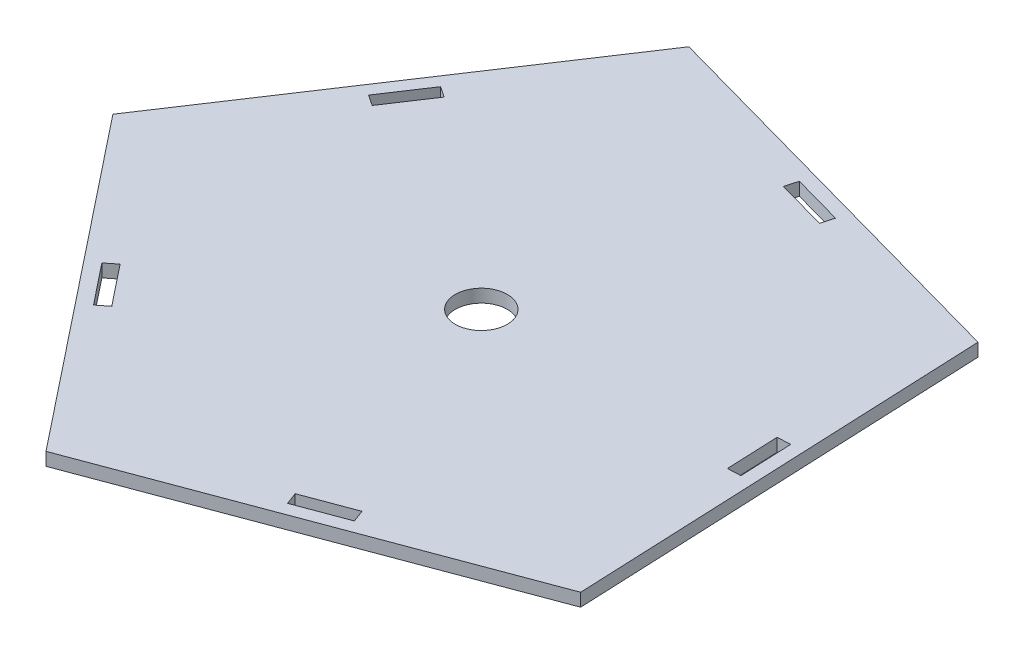
SolidWorks part; units mm, degrees
ref_plane "Front Plane" through (0, 0, 0) normal (0, 0, 1) x (1, 0, 0)
ref_plane "Top Plane" through (0, 0, 0) normal (0, 1, 0) x (1, 0, 0)
ref_plane "Right Plane" through (0, 0, 0) normal (1, 0, 0) x (0, 0, -1)
sketch "Sketch1" plane through (0, 0, 0) normal (0, 1, 0) x (1, 0, 0)
  line L1 (-20.8753, -32.8264) -> (-29.6171, 170.1854)
  line L2 (-29.6171, 170.1854) -> (-225.3943, 224.6055)
  line L3 (-225.3943, 224.6055) -> (-337.6493, 55.2271)
  line L4 (-337.6493, 55.2271) -> (-211.2496, -103.8746)
  line L5 (-211.2496, -103.8746) -> (-20.8753, -32.8264)
  circle A0 centre (-164.9571, 62.6634) radius 139.8404 construction
  dimension "D1" = 203.2
extrude "Boss-Extrude1" add sketch "Sketch1" along normal blind 6.35
sketch "Sketch2" plane through (0, 6.35, 0) normal (0, 1, 0) x (1, 0, 0)
  line L0 (-211.2496, -103.8746) -> (-20.8753, -32.8264) construction
  line L1 (-132.4014, -60.8926) -> (-108.6046, -52.0116)
  line L2 (-132.4014, -60.8926) -> (-130.1811, -66.8418)
  line L3 (-130.1811, -66.8418) -> (-106.3843, -57.9608)
  line L4 (-108.6046, -52.0116) -> (-106.3843, -57.9608)
  line L5 (-337.6493, 55.2271) -> (-211.2496, -103.8746) construction
  line L6 (-277.3775, -10.4299) -> (-261.5776, -30.3176)
  line L7 (-277.3775, -10.4299) -> (-272.4056, -6.4799)
  line L8 (-272.4056, -6.4799) -> (-256.6056, -26.3676)
  line L9 (-261.5776, -30.3176) -> (-256.6056, -26.3676)
  line L10 (-225.3943, 224.6055) -> (-337.6493, 55.2271) construction
  line L11 (-283.2447, 125.8222) -> (-277.9516, 122.3143)
  line L12 (-283.2447, 125.8222) -> (-269.2128, 146.9945)
  line L13 (-269.2128, 146.9945) -> (-263.9197, 143.4866)
  line L14 (-277.9516, 122.3143) -> (-263.9197, 143.4866)
  line L15 (-29.6171, 170.1854) -> (-225.3943, 224.6055) construction
  line L16 (-141.4424, 194.6787) -> (-116.9703, 187.8762)
  line L17 (-141.4424, 194.6787) -> (-143.143, 188.5607)
  line L18 (-143.143, 188.5607) -> (-118.6709, 181.7582)
  line L19 (-116.9703, 187.8762) -> (-118.6709, 181.7582)
  line L20 (-20.8753, -32.8264) -> (-29.6171, 170.1854) construction
  line L21 (-38.4808, 80.8214) -> (-32.1367, 81.0946)
  line L22 (-38.4808, 80.8214) -> (-37.3881, 55.4449)
  line L23 (-37.3881, 55.4449) -> (-31.0439, 55.7181)
  line L24 (-32.1367, 81.0946) -> (-31.0439, 55.7181)
  point P27 (-117.8206, 184.8172)
  dimension "D1" = 6.35
  dimension "D2" = 25.4
  dimension "D3" = 6.35
  dimension "D4" = 88.9
  dimension "D5" = 25.4
  dimension "D6" = 6.35
  dimension "D7" = 6.35
  dimension "D8" = 88.9
  dimension "D9" = 25.4
  dimension "D10" = 6.35
  dimension "D11" = 6.35
  dimension "D12" = 88.9
  dimension "D13" = 6.35
  dimension "D14" = 25.4
  dimension "D15" = 6.35
  dimension "D16" = 88.9
  dimension "D17" = 6.35
  dimension "D18" = 25.4
  dimension "D19" = 6.35
  dimension "D20" = 88.9
extrude "Cut-Extrude1" cut sketch "Sketch2" against normal through all
sketch "Sketch3" plane through (0, 6.35, 0) normal (0, 1, 0) x (1, 0, 0)
  line L0 (-225.3943, 224.6055) -> (-116.0624, -68.3505) construction
  line L1 (-211.2496, -103.8746) -> (-20.8753, -32.8264) construction
  line L2 (-337.6493, 55.2271) -> (-25.2462, 68.6795) construction
  line L4 (-29.6171, 170.1854) -> (-274.4495, -24.3237) construction
  line L5 (-337.6493, 55.2271) -> (-211.2496, -103.8746) construction
  line L6 (-20.8753, -32.8264) -> (-29.6171, 170.1854) construction
  circle A0 centre (-164.9571, 62.6634) radius 12.7
  point P21 (-164.9571, 62.6634)
extrude "Cut-Extrude2" cut sketch "Sketch3" against normal through all
sketch "Sketch4" plane through (0, 6.35, 0) normal (0, 1, 0) x (1, 0, 0)
  line L20 (-29.4236, 170.3392) -> (-225.4807, 224.8372)
  line L21 (-20.6692, -32.963) -> (-29.4236, 170.3392)
  line L22 (-211.3158, -104.1127) -> (-20.6692, -32.963)
  line L23 (-337.8963, 55.2165) -> (-211.3158, -104.1127)
  line L24 (-225.4807, 224.8372) -> (-337.8963, 55.2165)
  line L25 (-29.4236, 170.3392) -> (-225.4807, 224.8372)
  line L26 (-20.6692, -32.963) -> (-29.4236, 170.3392)
  line L27 (-211.3158, -104.1127) -> (-20.6692, -32.963)
  line L28 (-337.8963, 55.2165) -> (-211.3158, -104.1127)
  line L29 (-225.4807, 224.8372) -> (-337.8963, 55.2165)
  line L35 (-29.23, 170.493) -> (-225.5672, 225.0688)
  line L36 (-225.5672, 225.0688) -> (-338.1433, 55.2059)
  line L37 (-338.1433, 55.2059) -> (-211.382, -104.3509)
  line L38 (-211.382, -104.3509) -> (-20.4631, -33.0996)
  line L39 (-261.5454, -30.0366) -> (-256.8867, -26.3354)
  line L40 (-272.4378, -6.7609) -> (-277.0965, -10.462)
  line L41 (-277.0965, -10.462) -> (-261.5454, -30.0366)
  line L42 (-256.8867, -26.3354) -> (-272.4378, -6.7609)
  line L43 (-261.5454, -30.0366) -> (-256.8867, -26.3354)
  line L44 (-272.4378, -6.7609) -> (-277.0965, -10.462)
  line L45 (-277.0965, -10.462) -> (-261.5454, -30.0366)
  line L46 (-256.8867, -26.3354) -> (-272.4378, -6.7609)
  line L47 (-20.4631, -33.0996) -> (-29.23, 170.493)
  line L62 (-106.6416, -57.8433) -> (-108.722, -52.2689)
  line L63 (-132.144, -61.0101) -> (-130.0636, -66.5845)
  line L64 (-130.0636, -66.5845) -> (-106.6416, -57.8433)
  line L65 (-108.722, -52.2689) -> (-132.144, -61.0101)
  line L66 (-106.6416, -57.8433) -> (-108.722, -52.2689)
  line L67 (-132.144, -61.0101) -> (-130.0636, -66.5845)
  line L68 (-130.0636, -66.5845) -> (-106.6416, -57.8433)
  line L69 (-108.722, -52.2689) -> (-132.144, -61.0101)
  line L80 (-32.3279, 80.8861) -> (-38.2724, 80.6302)
  line L81 (-37.1969, 55.6533) -> (-31.2524, 55.9093)
  line L82 (-31.2524, 55.9093) -> (-32.3279, 80.8861)
  line L83 (-38.2724, 80.6302) -> (-37.1969, 55.6533)
  line L84 (-32.3279, 80.8861) -> (-38.2724, 80.6302)
  line L85 (-37.1969, 55.6533) -> (-31.2524, 55.9093)
  line L86 (-31.2524, 55.9093) -> (-32.3279, 80.8861)
  line L87 (-38.2724, 80.6302) -> (-37.1969, 55.6533)
  line L98 (-264.1969, 143.4303) -> (-269.1566, 146.7173)
  line L99 (-278.0078, 122.5915) -> (-264.1969, 143.4303)
  line L100 (-282.9675, 125.8784) -> (-278.0078, 122.5915)
  line L101 (-269.1566, 146.7173) -> (-282.9675, 125.8784)
  line L102 (-264.1969, 143.4303) -> (-269.1566, 146.7173)
  line L103 (-278.0078, 122.5915) -> (-264.1969, 143.4303)
  line L104 (-282.9675, 125.8784) -> (-278.0078, 122.5915)
  line L105 (-269.1566, 146.7173) -> (-282.9675, 125.8784)
  circle A2 centre (-164.9571, 62.6634) radius 12.5
  circle A3 centre (-164.9571, 62.6634) radius 12.5
  dimension "D1" = 0.2
  dimension "D2" = 0.2
  dimension "D3" = 0.2
  dimension "D4" = 0.2
  dimension "D5" = 0.2
  dimension "D6" = 0.2
  dimension "D7" = 0.2
